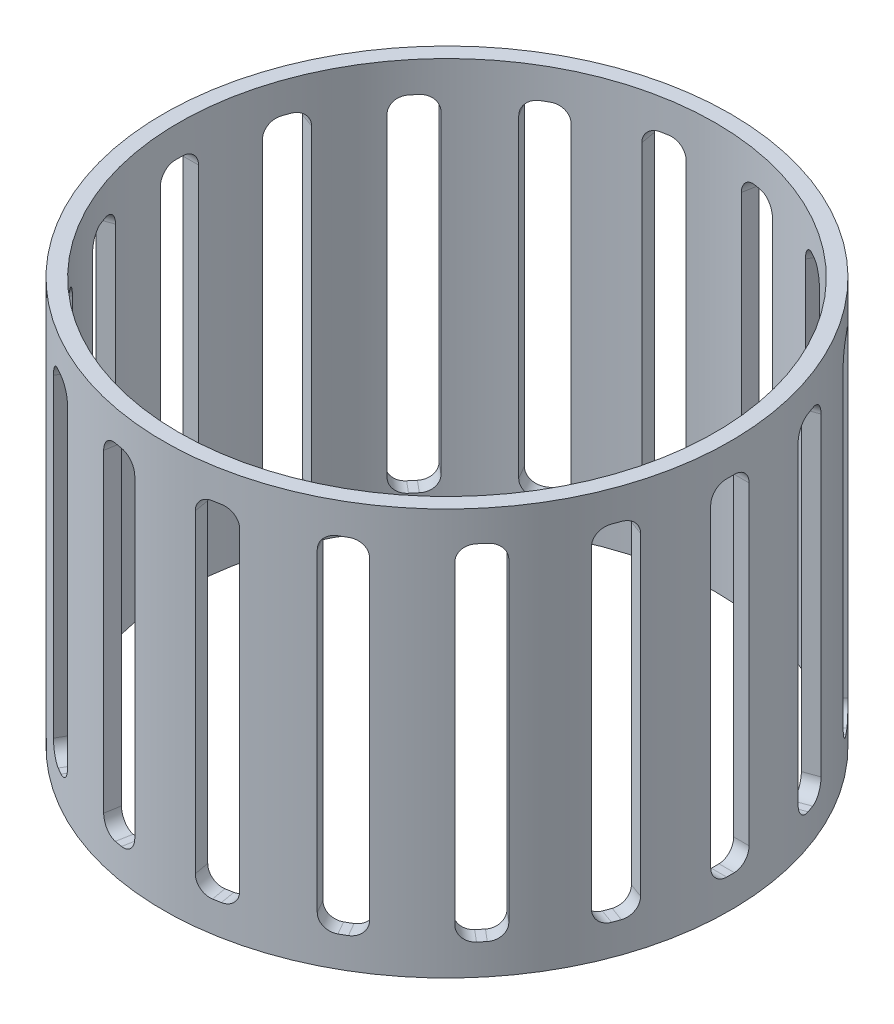
SolidWorks part; units mm, degrees
material "6061-T6 (SS)"
ref_plane "Płaszczyzna przednia" through (0, 0, 0) normal (0, 0, 1) x (1, 0, 0)
ref_plane "Płaszczyzna górna" through (0, 0, 0) normal (0, 1, 0) x (1, 0, 0)
ref_plane "Płaszczyzna prawa" through (0, 0, 0) normal (1, 0, 0) x (0, 0, -1)
sketch "Szkic1" plane through (0, 0, 0) normal (0, 0, 1) x (1, 0, 0)
  line L0 (0, -11.5417) -> (0, 16.5417) construction
  line L1 (-37, 26.5) -> (-37, -26.5)
  line L2 (-37, -26.5) -> (-35, -26.5)
  line L3 (-35, -26.5) -> (-35, 26.5)
  line L4 (-35, 26.5) -> (-37, 26.5)
  point P5 (-37, 0)
  dimension "D1" = 2
  dimension "D2" = 70
  dimension "D3" = 53
revolve "Obrót1" add sketch "Szkic1" angle 360 about L0
sketch "Szkic2" plane through (0, 0, 0) normal (1, 0, 0) x (0, 0, -1)
  line L0 (35, 26.5) -> (-35, 26.5) construction
  line L1 (37, 26.5) -> (-37, 26.5) construction
  line L2 (-37, -26.5) -> (37, -26.5) construction
  line L3 (-35, -26.5) -> (35, -26.5) construction
  line L4 (35, 26.5) -> (-35, 26.5)
  line L5 (37, 26.5) -> (-37, 26.5)
  line L6 (-37, -26.5) -> (37, -26.5)
  line L7 (-35, -26.5) -> (35, -26.5)
  line L8 (0, 26.5) -> (0, -26.5) construction
  line L9 (2.5, 22.5) -> (-2.5, 22.5)
  line L10 (-2.5, 22.5) -> (-2.5, -22.5)
  line L11 (-2.5, -22.5) -> (2.5, -22.5)
  line L12 (2.5, -22.5) -> (2.5, 22.5)
  point P12 (-2.5, 0)
  point P15 (0, 22.5)
  dimension "D1" = 5
  dimension "D2" = 4
extrude "Wytnij-wyciągnięcie1" cut sketch "Szkic2" against normal up to surface (36.9154 mm away) contours L8 L9 L10 L11 | L9 L8 L11 L12
fillet "Zaokrąglenie1" radius 2 4 edges at (-35.913, -22.5, -2.5) (-35.913, -22.5, 2.5) (-35.913, 22.5, -2.5) (-35.913, 22.5, 2.5)
pattern_circular "Szyk kołowy1" count 18 over 360 about axis through (0, 0, 0) along (0, 1, 0) of "Wytnij-wyciągnięcie1", "Zaokrąglenie1"
